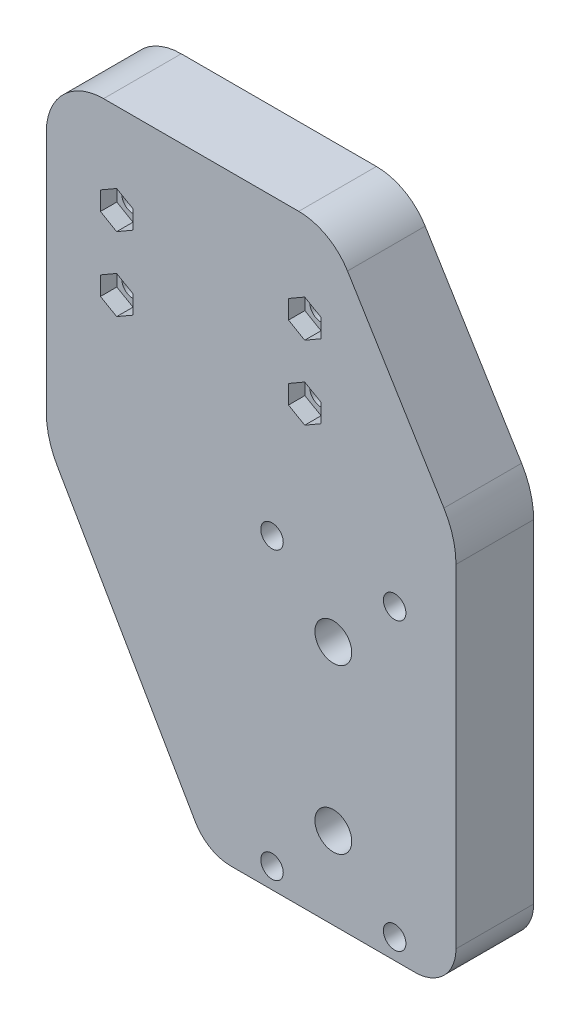
SolidWorks part; units mm, degrees
ref_plane "Front Plane" through (0, 0, 0) normal (0, 0, 1) x (1, 0, 0)
ref_plane "Top Plane" through (0, 0, 0) normal (0, 1, 0) x (1, 0, 0)
ref_plane "Right Plane" through (0, 0, 0) normal (1, 0, 0) x (0, 0, -1)
sketch "Sketch1" plane through (0, 0, 0) normal (0, 0, 1) x (1, 0, 0)
  line L0 (-130, 510) -> (13.8884, 510) construction
  line L1 (-170.2, 540.8246) -> (-129.3094, 470)
  line L2 (-116.2253, 607) -> (-90, 564.2553)
  line L15 (-90, 473) -> (-90, 564.2553)
  line L16 (-90, 473) -> (-90, 547) construction
  line L24 (-170.2, 540.8246) -> (-170.2, 607)
  line L25 (-170.2, 607) -> (-116.2253, 607)
  line L183 (-129.3094, 470) -> (-93, 470)
  arc A1 (-113.8, 602.2) -> (-116.8, 605.2) centre (-116.8, 602.2) ccw construction
  arc A13 (-90, 473) -> (-93, 470) centre (-93, 473) cw
extrude "Boss-Extrude1" add sketch "Sketch1" along normal blind 19
fillet "Fillet1" radius 10 3 edges at (-129.3094, 470, 9.5) (-170.2, 540.8246, 9.5) (-90, 564.2553, 9.5)
sketch "Sketch2" plane through (0, 0, 19) normal (0, 0, 1) x (1, 0, 0)
  circle A0 centre (-139, 577) radius 20
  dimension "D1" = 40
hole_wizard "M5 Clearance Hole2" positions "Sketch5" profile "Sketch6" hole size "M5" standard "ISO" end condition through all
sketch "Sketch5" plane through (0, 0, 0) normal (0, 0, -1) x (-1, 0, 0)
  line L1 (117, 595) -> (117, 577)
  line L2 (117, 595) -> (163, 595)
  line L3 (163, 595) -> (163, 577)
  line L4 (117, 577) -> (163, 577)
  circle A1 centre (117, 595) radius 2.1
  point P2 (117, 595)
  point P4 (117, 577)
  point P6 (163, 577)
  point P8 (163, 595)
  dimension "D1" = 18
  dimension "D2" = 46
  dimension "D3" = 46
  dimension "D4" = 18
sketch "Sketch6" plane through (-117, 595, 0) normal (1, 0, 0) x (0, 1, 0)
  line L0 (0, 0) -> (0, 19)
  line L1 (0, 19) -> (2.75, 19)
  line L2 (2.75, 19) -> (2.75, 0)
  line L5 (2.75, 0) -> (0, 0)
  line L11 (0, -6.35) -> (0, 107.95) construction
  dimension "Thru Hole Dia." = 5.5
  dimension "Thru Hole Depth" = 19
hole_wizard "M5 Clearance Hole1" positions "Sketch7" profile "Sketch8" hole size "M5" standard "ISO" end condition through all
sketch "Sketch7" plane through (0, 0, 19) normal (0, 0, 1) x (1, 0, 0)
  point P0 (-95, 545)
  point P2 (-125, 545)
  point P4 (-125, 475)
  point P6 (-95, 475)
  point P8 (-110, 490)
  point P10 (-110, 530)
sketch "Sketch8" plane through (-95, 545, 19) normal (1, 0, 0) x (0, -1, 0)
  line L0 (0, 0) -> (0, 19)
  line L1 (0, 19) -> (2.75, 19)
  line L2 (2.75, 19) -> (2.75, 0)
  line L5 (2.75, 0) -> (0, 0)
  line L11 (0, -6.35) -> (0, 107.95) construction
  dimension "Thru Hole Dia." = 5.5
  dimension "Thru Hole Depth" = 19
hole_wizard "Tap Drill for M5 Tap2" [suppressed] positions "Sketch9" profile "Sketch10" hole size "M5" standard "ISO"
sketch "Sketch9" plane through (0, 0, 19) normal (0, 0, 1) x (1, 0, 0)
  point P0 (-163.57, 553.43)
  point P2 (-163.57, 600.57)
  point P4 (-116.43, 553.43)
  point P6 (-116.43, 600.57)
sketch "Sketch10" plane through (-163.57, 553.43, 19) normal (1, 0, 0) x (0, -1, 0)
  line L0 (0, 0) -> (0, 19)
  line L1 (0, 19) -> (2.1, 19)
  line L2 (2.1, 19) -> (2.1, 0)
  line L5 (2.1, 0) -> (0, 0)
  line L11 (0, -6.35) -> (0, 107.95) construction
  dimension "Thru Hole Dia." = 4.2
  dimension "Thru Hole Depth" = 19
fillet "Fillet2" radius 4 2 edges at (-116.2253, 607, 9.5) (-170.2, 607, 9.5)
sketch "Sketch11" plane through (0, 0, 19) normal (0, 0, 1) x (1, 0, 0)
  line L6 (-135.0829, 470) -> (-90, 470)
  line L7 (-80, 480) -> (-80, 561.4321)
  line L8 (-82.9528, 571.8912) -> (-106.531, 610.3213)
  line L9 (-118.464, 617) -> (-166.2, 617)
  line L10 (-180.2, 603) -> (-180.2, 543.5041)
  line L11 (-177.5205, 533.5041) -> (-143.7432, 475)
  line L12 (-135.0829, 470) -> (-90, 470)
  line L13 (-80, 480) -> (-80, 561.4321)
  line L14 (-82.9528, 571.8912) -> (-106.531, 610.3213)
  line L15 (-118.464, 617) -> (-166.2, 617)
  line L16 (-180.2, 603) -> (-180.2, 543.5041)
  line L17 (-177.5205, 533.5041) -> (-143.7432, 475)
  line L18 (-91.4764, 566.6616) -> (-115.0546, 605.0918)
  line L19 (-118.464, 607) -> (-166.2, 607)
  line L20 (-170.2, 603) -> (-170.2, 543.5041)
  line L21 (-168.8603, 538.5041) -> (-132.1962, 475)
  line L22 (-123.5359, 470) -> (-93, 470)
  line L23 (-90, 473) -> (-90, 561.4321)
  line L24 (-91.4764, 566.6616) -> (-115.0546, 605.0918)
  line L25 (-118.464, 607) -> (-166.2, 607)
  line L26 (-170.2, 603) -> (-170.2, 543.5041)
  line L27 (-168.8603, 538.5041) -> (-132.1962, 475)
  line L28 (-123.5359, 470) -> (-93, 470)
  line L29 (-90, 473) -> (-90, 561.4321)
  arc A6 (-143.7432, 475) -> (-135.0829, 470) centre (-135.0829, 480) ccw
  arc A7 (-90, 470) -> (-80, 480) centre (-90, 480) ccw
  arc A8 (-80, 561.4321) -> (-82.9528, 571.8912) centre (-100, 561.4321) ccw
  arc A9 (-106.531, 610.3213) -> (-118.464, 617) centre (-118.464, 603) ccw
  arc A10 (-166.2, 617) -> (-180.2, 603) centre (-166.2, 603) ccw
  arc A11 (-180.2, 543.5041) -> (-177.5205, 533.5041) centre (-160.2, 543.5041) ccw
  arc A12 (-143.7432, 475) -> (-135.0829, 470) centre (-135.0829, 480) ccw
  arc A13 (-90, 470) -> (-80, 480) centre (-90, 480) ccw
  arc A14 (-80, 561.4321) -> (-82.9528, 571.8912) centre (-100, 561.4321) ccw
  arc A15 (-106.531, 610.3213) -> (-118.464, 617) centre (-118.464, 603) ccw
  arc A16 (-166.2, 617) -> (-180.2, 603) centre (-166.2, 603) ccw
  arc A17 (-180.2, 543.5041) -> (-177.5205, 533.5041) centre (-160.2, 543.5041) ccw
  arc A18 (-115.0546, 605.0918) -> (-118.464, 607) centre (-118.464, 603) ccw
  arc A19 (-166.2, 607) -> (-170.2, 603) centre (-166.2, 603) ccw
  arc A20 (-170.2, 543.5041) -> (-168.8603, 538.5041) centre (-160.2, 543.5041) ccw
  arc A21 (-132.1962, 475) -> (-123.5359, 470) centre (-123.5359, 480) ccw
  arc A22 (-93, 470) -> (-90, 473) centre (-93, 473) ccw
  arc A23 (-90, 561.4321) -> (-91.4764, 566.6616) centre (-100, 561.4321) ccw
  arc A24 (-115.0546, 605.0918) -> (-118.464, 607) centre (-118.464, 603) ccw
  arc A25 (-166.2, 607) -> (-170.2, 603) centre (-166.2, 603) ccw
  arc A26 (-170.2, 543.5041) -> (-168.8603, 538.5041) centre (-160.2, 543.5041) ccw
  arc A27 (-132.1962, 475) -> (-123.5359, 470) centre (-123.5359, 480) ccw
  arc A28 (-93, 470) -> (-90, 473) centre (-93, 473) ccw
  arc A29 (-90, 561.4321) -> (-91.4764, 566.6616) centre (-100, 561.4321) ccw
  dimension "D1" = 0
  dimension "D2" = 0
extrude "Boss-Extrude2" add sketch "Sketch11" against normal up to surface (19 mm away)
hole_wizard "M8 Clearance Hole1" positions "Sketch12" profile "Sketch13" hole size "M8" standard "ISO" end condition through all
sketch "Sketch12" plane through (0, 0, 19) normal (0, 0, 1) x (1, 0, 0)
  point P0 (-110, 530)
  point P3 (-110, 490)
sketch "Sketch13" plane through (-110, 530, 19) normal (1, 0, 0) x (0, -1, 0)
  line L0 (0, 0) -> (0, 19)
  line L1 (0, 19) -> (4.5, 19)
  line L2 (4.5, 19) -> (4.5, 0)
  line L5 (4.5, 0) -> (0, 0)
  line L11 (0, -6.35) -> (0, 107.95) construction
  dimension "Thru Hole Dia." = 9
  dimension "Thru Hole Depth" = 19
extrude "Cut-Extrude1" [suppressed] cut sketch "Sketch2" against normal through all
sketch "Sketch14" plane through (0, 0, 19) normal (0, 0, 1) x (1, 0, 0)
  line L0 (-177.5205, 533.5041) -> (-143.7432, 475)
  line L1 (-180.2, 603) -> (-180.2, 543.5041)
  line L2 (-118.464, 617) -> (-166.2, 617)
  line L3 (-82.9528, 571.8912) -> (-106.531, 610.3213)
  line L4 (-80, 480) -> (-80, 561.4321)
  line L5 (-135.0829, 470) -> (-90, 470)
  circle A0 centre (-110, 530) radius 4.5
  circle A1 centre (-95, 545) radius 2.75
  circle A2 centre (-165, 595) radius 2.1
  circle A3 centre (-165, 577) radius 2.1
  circle A4 centre (-119, 577) radius 2.1
  circle A5 centre (-119, 595) radius 2.1
  circle A6 centre (-95, 475) radius 2.75
  circle A7 centre (-125, 475) radius 2.75
  circle A8 centre (-125, 545) radius 2.75
  circle A9 centre (-110, 490) radius 4.5
  arc A10 (-180.2, 543.5041) -> (-177.5205, 533.5041) centre (-160.2, 543.5041) ccw
  arc A11 (-166.2, 617) -> (-180.2, 603) centre (-166.2, 603) ccw
  arc A12 (-106.531, 610.3213) -> (-118.464, 617) centre (-118.464, 603) ccw
  arc A13 (-80, 561.4321) -> (-82.9528, 571.8912) centre (-100, 561.4321) ccw
  arc A14 (-90, 470) -> (-80, 480) centre (-90, 480) ccw
  arc A15 (-143.7432, 475) -> (-135.0829, 470) centre (-135.0829, 480) ccw
sketch "Sketch15" plane through (0, 0, 19) normal (0, 0, 1) x (1, 0, 0)
  line L0 (-140, 595) -> (-140, 577) construction
  line L1 (-166.96, 579.2863) -> (-166.96, 574.7137)
  line L2 (-166.96, 574.7137) -> (-163, 572.4274)
  line L3 (-163, 572.4274) -> (-159.04, 574.7137)
  line L4 (-159.04, 574.7137) -> (-159.04, 579.2863)
  line L5 (-159.04, 579.2863) -> (-163, 581.5726)
  line L6 (-163, 581.5726) -> (-166.96, 579.2863)
  line L7 (-163, 577) -> (-117, 577) construction
  line L8 (-163, 577) -> (-163, 595) construction
  line L9 (-163, 595) -> (-117, 595) construction
  line L10 (-117, 577) -> (-117, 595) construction
  line L11 (-117, 586) -> (-163, 586) construction
  line L12 (-120.96, 579.2863) -> (-120.96, 574.7137)
  line L13 (-120.96, 574.7137) -> (-117, 572.4274)
  line L14 (-117, 572.4274) -> (-113.04, 574.7137)
  line L15 (-113.04, 574.7137) -> (-113.04, 579.2863)
  line L16 (-113.04, 579.2863) -> (-117, 581.5726)
  line L17 (-117, 581.5726) -> (-120.96, 579.2863)
  line L18 (-113.04, 592.7137) -> (-117, 590.4274)
  line L19 (-117, 590.4274) -> (-120.96, 592.7137)
  line L20 (-120.96, 592.7137) -> (-120.96, 597.2863)
  line L21 (-120.96, 597.2863) -> (-117, 599.5726)
  line L22 (-117, 599.5726) -> (-113.04, 597.2863)
  line L23 (-113.04, 597.2863) -> (-113.04, 592.7137)
  line L24 (-163, 590.4274) -> (-166.96, 592.7137)
  line L25 (-159.04, 592.7137) -> (-163, 590.4274)
  line L26 (-159.04, 597.2863) -> (-159.04, 592.7137)
  line L27 (-163, 599.5726) -> (-159.04, 597.2863)
  line L28 (-166.96, 597.2863) -> (-163, 599.5726)
  line L29 (-166.96, 592.7137) -> (-166.96, 597.2863)
  circle A0 centre (-163, 577) radius 3.96 construction
  point P18 (-140, 586)
  dimension "D1" = 7.92
  dimension "D2" = 2
extrude "Cut-Extrude2" cut sketch "Sketch15" against normal blind 4
sketch "Sketch16" plane through (0, 0, 0) normal (0, 0, -1) x (-1, 0, 0)
  circle A0 centre (140, 577) radius 10
  dimension "D1" = 20
extrude "Cut-Extrude3" cut sketch "Sketch16" against normal blind 5
